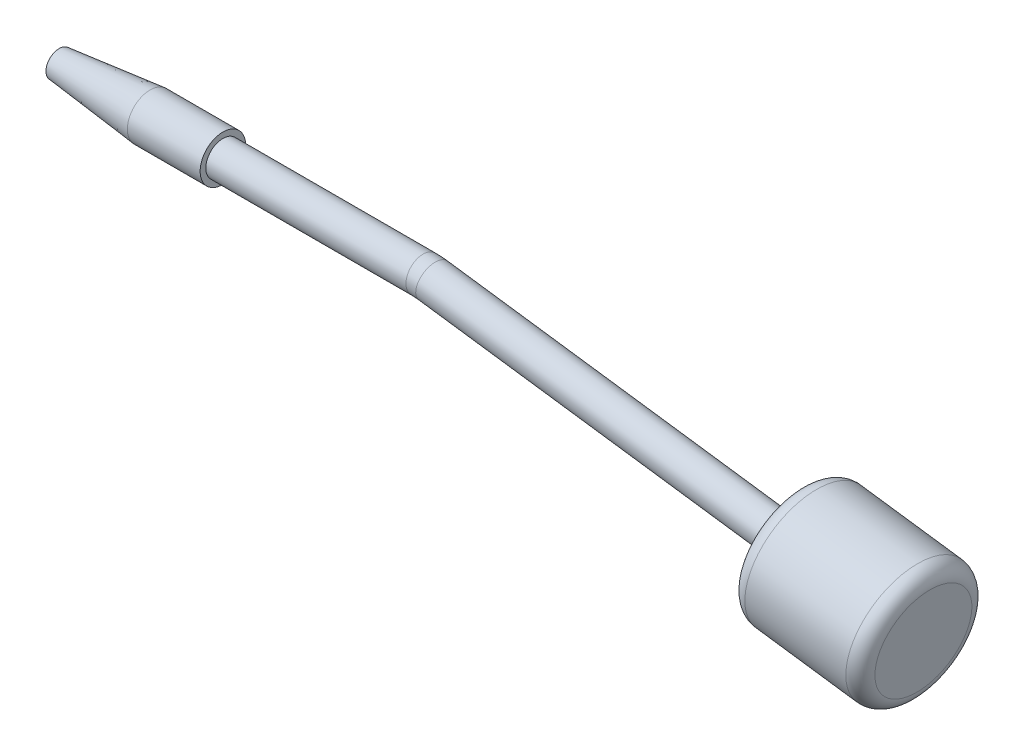
SolidWorks part; units mm, degrees
ref_plane "Front Plane" through (0, 0, 0) normal (0, 0, 1) x (1, 0, 0)
ref_plane "Top Plane" through (0, 0, 0) normal (0, 1, 0) x (1, 0, 0)
ref_plane "Right Plane" through (0, 0, 0) normal (1, 0, 0) x (0, 0, -1)
sketch "Sketch1" plane through (0, 0, 0) normal (0, 0, 1) x (1, 0, 0)
  line L0 (0, 0) -> (-63.5, 0) construction
  line L1 (-63.5, -0.7938) -> (-63.5, -2.286)
  line L2 (-63.5, -2.286) -> (-47.625, -3.9688)
  line L3 (-34.925, -3.9688) -> (-34.925, -2.9845)
  line L4 (-34.925, -2.9845) -> (0, -2.9845)
  line L5 (0, -0.7938) -> (0, -2.9845)
  line L6 (-34.925, -3.9688) -> (-47.625, -3.9688)
  line L7 (-63.5, -0.7938) -> (0, -0.7938)
  dimension "D1" = 28.575
  dimension "D2" = 63.5
  dimension "D3" = 5.969
  dimension "D4" = 4.572
  dimension "D5" = 7.9375
  dimension "D6" = 12.7
  dimension "D7" = 1.5875
revolve "Revolve1" add sketch "Sketch1" angle 360 about L0
sketch "Sketch2" plane through (0, 0, 0) normal (0, 0, 1) x (1, 0, 0)
  line L0 (1.7236, -0.1175) -> (64.6361, -8.7354)
  line L1 (-34.925, -2.9845) -> (0, -2.9845) construction
  line L2 (0, 0) -> (-34.925, 0) construction
  line L3 (-34.925, -2.9845) -> (-34.925, 2.9845) construction
  arc A0 (0, 0) -> (1.7236, -0.1175) centre (0, -12.7) cw
  dimension "D1" = 12.7
  dimension "D2" = 172.2
  dimension "D3" = 63.5
sweep "Sweep1" add path "Sketch2" circular profile diameter 5.969 parameters "D3"=5.969
sketch "Sketch15" plane through (0, 0, 0) normal (0, 0, 1) x (1, 0, 0)
  line L0 (64.6361, -8.7354) -> (87.2846, -11.8379) construction
  line L1 (64.231, -11.6923) -> (65.0411, -5.7786) construction
  line L2 (87.2846, -11.8379) -> (85.8023, -22.6588)
  line L3 (85.8023, -22.6588) -> (63.1538, -19.5564)
  line L4 (63.1538, -19.5564) -> (64.6361, -8.7354)
  line L6 (1.3185, -3.0744) -> (64.231, -11.6923) construction
  line L7 (64.6361, -8.7354) -> (87.2846, -11.8379)
  dimension "D1" = 21.844
  dimension "D2" = 22.86
revolve "Revolve2" add sketch "Sketch15" angle 360 about L0
fillet "Fillet1" radius 2.54 2 edges at (85.8023, -22.6588, 0) (63.1538, -19.5564, 0)
